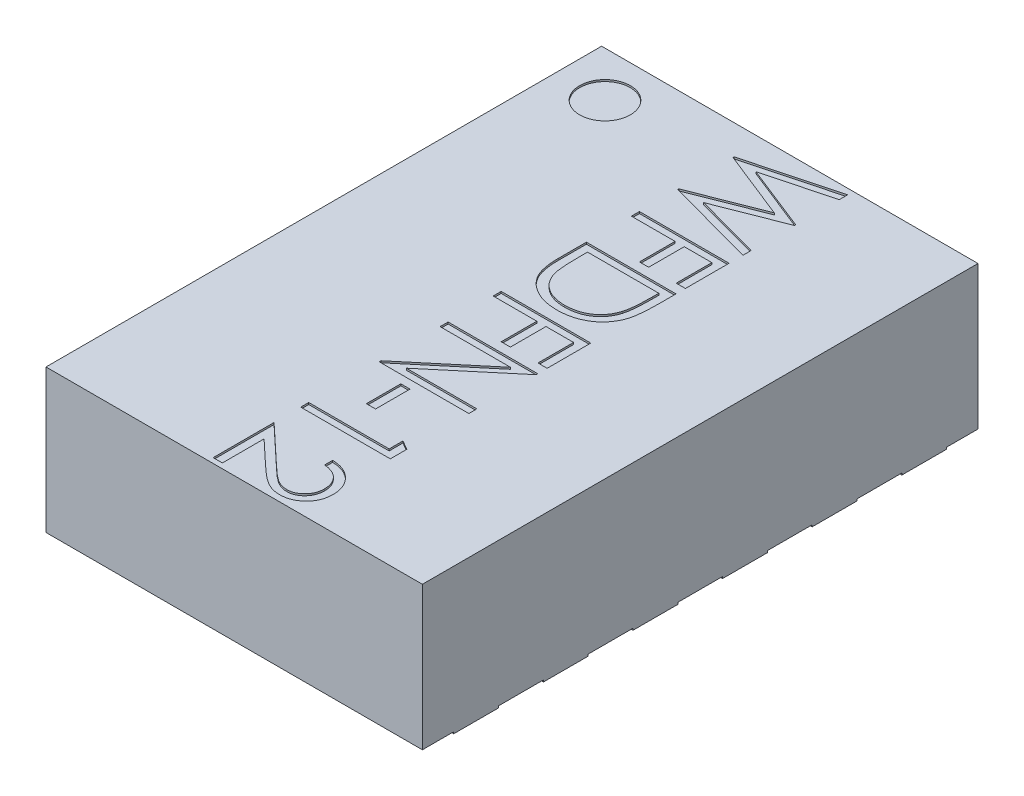
SolidWorks part; units mm, degrees
ref_plane "Front Plane" through (0, 0, 0) normal (0, 0, 1) x (1, 0, 0)
ref_plane "Top Plane" through (0, 0, 0) normal (0, 1, 0) x (1, 0, 0)
ref_plane "Right Plane" through (0, 0, 0) normal (1, 0, 0) x (0, 0, -1)
sketch "Sketch1" plane through (0, 0, 0) normal (0, 1, 0) x (1, 0, 0)
  line L1 (-1.05, 1.55) -> (1.05, 1.55)
  line L2 (-1.05, 1.55) -> (-1.05, -1.55)
  line L3 (-1.05, -1.55) -> (1.05, -1.55)
  line L4 (1.05, 1.55) -> (1.05, -1.55)
  line L5 (-1.05, 1.55) -> (1.05, -1.55) construction
  line L6 (-1.05, -1.55) -> (1.05, 1.55) construction
  point P0 (0, 0)
  dimension "D1" = 2.1
  dimension "D2" = 3.1
extrude "Boss-Extrude1" add sketch "Sketch1" along normal blind 0.8
sketch "Sketch2" plane through (0, 0, 0) normal (0, -1, 0) x (1, 0, 0)
  line L0 (-1.05, -1.55) -> (-1.05, 1.55) construction
  line L1 (-1.05, -1.375) -> (-0.75, -1.375)
  line L2 (-1.05, -1.375) -> (-1.05, -1.125)
  line L3 (-1.05, -1.125) -> (-0.75, -1.125)
  line L4 (-0.75, -1.375) -> (-0.75, -1.125)
  line L5 (-0.75, -1.25) -> (-1.05, -1.25) construction
  line L6 (-1.05, -0.875) -> (-0.75, -0.875)
  line L7 (-1.05, -0.875) -> (-1.05, -0.625)
  line L8 (-1.05, -0.625) -> (-0.75, -0.625)
  line L9 (-0.75, -0.875) -> (-0.75, -0.625)
  line L10 (-0.75, -0.75) -> (-1.05, -0.75) construction
  line L11 (-1.05, -0.375) -> (-0.75, -0.375)
  line L12 (-1.05, -0.375) -> (-1.05, -0.125)
  line L13 (-1.05, -0.125) -> (-0.75, -0.125)
  line L14 (-0.75, -0.375) -> (-0.75, -0.125)
  line L15 (-0.75, -0.25) -> (-1.05, -0.25) construction
  line L16 (-1.05, 0.125) -> (-0.75, 0.125)
  line L17 (-1.05, 0.125) -> (-1.05, 0.375)
  line L18 (-1.05, 0.375) -> (-0.75, 0.375)
  line L19 (-0.75, 0.125) -> (-0.75, 0.375)
  line L20 (-0.75, 0.25) -> (-1.05, 0.25) construction
  line L21 (-1.05, 0.625) -> (-0.75, 0.625)
  line L22 (-1.05, 0.625) -> (-1.05, 0.875)
  line L23 (-1.05, 0.875) -> (-0.75, 0.875)
  line L24 (-0.75, 0.625) -> (-0.75, 0.875)
  line L25 (-0.75, 0.75) -> (-1.05, 0.75) construction
  line L26 (-1.05, 1.125) -> (-0.75, 1.125)
  line L27 (-1.05, 1.125) -> (-1.05, 1.375)
  line L28 (-1.05, 1.375) -> (-0.75, 1.375)
  line L29 (-0.75, 1.125) -> (-0.75, 1.375)
  line L30 (-0.75, 1.25) -> (-1.05, 1.25) construction
  line L31 (-0.75, 1.375) -> (-1.05, 1.55) construction
  line L32 (-0.75, -1.375) -> (-1.05, -1.55) construction
  line L33 (1.05, -1.55) -> (-1.05, -1.55) construction
  line L34 (0, 1.55) -> (0, -1.55) construction
  line L35 (-1.05, 1.55) -> (1.05, 1.55) construction
  line L36 (1.05, 0) -> (-1.05, 0) construction
  line L37 (1.05, 1.55) -> (1.05, -1.55) construction
  line L38 (0.75, -1.375) -> (1.05, -1.55) construction
  line L39 (0.75, 1.375) -> (1.05, 1.55) construction
  line L40 (0.75, 1.25) -> (1.05, 1.25) construction
  line L41 (0.75, 0.75) -> (1.05, 0.75) construction
  line L42 (0.75, 0.25) -> (1.05, 0.25) construction
  line L43 (0.75, -0.25) -> (1.05, -0.25) construction
  line L44 (0.75, -0.75) -> (1.05, -0.75) construction
  line L45 (0.75, -1.25) -> (1.05, -1.25) construction
  line L46 (0.75, 1.125) -> (0.75, 1.375)
  line L47 (1.05, 1.375) -> (0.75, 1.375)
  line L48 (1.05, 1.125) -> (1.05, 1.375)
  line L49 (1.05, 1.125) -> (0.75, 1.125)
  line L50 (0.75, 0.625) -> (0.75, 0.875)
  line L51 (1.05, 0.875) -> (0.75, 0.875)
  line L52 (1.05, 0.625) -> (1.05, 0.875)
  line L53 (1.05, 0.625) -> (0.75, 0.625)
  line L54 (0.75, 0.125) -> (0.75, 0.375)
  line L55 (1.05, 0.375) -> (0.75, 0.375)
  line L56 (1.05, 0.125) -> (1.05, 0.375)
  line L57 (1.05, 0.125) -> (0.75, 0.125)
  line L58 (0.75, -0.375) -> (0.75, -0.125)
  line L59 (1.05, -0.125) -> (0.75, -0.125)
  line L60 (1.05, -0.375) -> (1.05, -0.125)
  line L61 (1.05, -0.375) -> (0.75, -0.375)
  line L62 (0.75, -0.875) -> (0.75, -0.625)
  line L63 (1.05, -0.625) -> (0.75, -0.625)
  line L64 (1.05, -0.875) -> (1.05, -0.625)
  line L65 (1.05, -0.875) -> (0.75, -0.875)
  line L66 (0.75, -1.375) -> (0.75, -1.125)
  line L67 (1.05, -1.125) -> (0.75, -1.125)
  line L68 (1.05, -1.375) -> (1.05, -1.125)
  line L69 (1.05, -1.375) -> (0.75, -1.375)
  line L70 (-0.5, 0) -> (-0.5, -1.125)
  line L71 (-0.5, 1.325) -> (0.5, 1.325)
  line L72 (-0.5, 1.325) -> (-0.5, 0)
  line L73 (-0.2731, -1.325) -> (0.5, -1.325)
  line L74 (0.5, 1.325) -> (0.5, -1.325)
  line L77 (-0.5, -1.125) -> (-0.2731, -1.325)
  point P89 (0, 0)
  point P92 (0, 1.325)
  point P96 (0.5, 0)
  dimension "D1" = 0.25
  dimension "D2" = 0.3
  dimension "D4" = 0.5
  dimension "D5" = 1
  dimension "D6" = 2.65
  dimension "D3" = 6
extrude "Boss-Extrude2" add sketch "Sketch2" along normal blind 0.01
sketch "Sketch3" plane through (0, 0.8, 0) normal (0, 1, 0) x (1, 0, 0)
  line L0 (-0.1455, 1.55) -> (-0.1455, -1.5218) construction
  line L1 (1.05, 1.55) -> (-1.05, 1.55) construction
  circle A0 centre (-0.7793, 1.2982) radius 0.1415
  text T0 "WFDFN-12" font "Century Gothic" height 0.5
extrude "Cut-Extrude1" cut sketch "Sketch3" against normal blind 0.01
